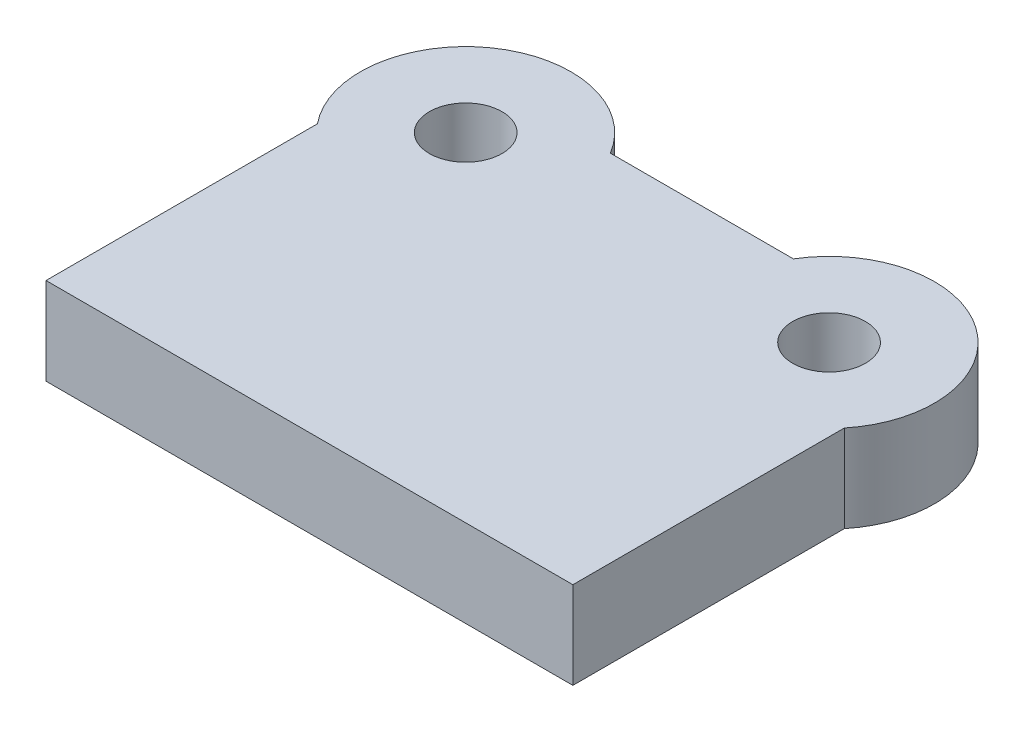
SolidWorks part; units mm, degrees
ref_plane "Front Plane" through (0, 0, 0) normal (0, 0, 1) x (1, 0, 0)
ref_plane "Top Plane" through (0, 0, 0) normal (0, 1, 0) x (1, 0, 0)
ref_plane "Right Plane" through (0, 0, 0) normal (1, 0, 0) x (0, 0, -1)
sketch "Sketch1" plane through (0, 0, 0) normal (0, 1, 0) x (1, 0, 0)
  line L0 (72.5, 0) -> (-72.5, 0)
  line L1 (-72.5, 0) -> (-72.5, 74.7038)
  line L2 (0, 0) -> (0, 108) construction
  line L3 (25.1807, 108) -> (-25.1807, 108)
  line L4 (72.5, 0) -> (72.5, 74.7038)
  arc A0 (-25.1807, 108) -> (-72.5, 74.7038) centre (-50, 93) ccw
  circle A1 centre (-50, 93) radius 10
  circle A2 centre (50, 93) radius 10
  arc A3 (25.1807, 108) -> (72.5, 74.7038) centre (50, 93) cw
  dimension "D3" = 58
  dimension "D4" = 20
  dimension "D1" = 145
  dimension "D2" = 100
  dimension "D5" = 93
  dimension "D6" = 108
extrude "Boss-Extrude1" add sketch "Sketch1" along normal blind 24
